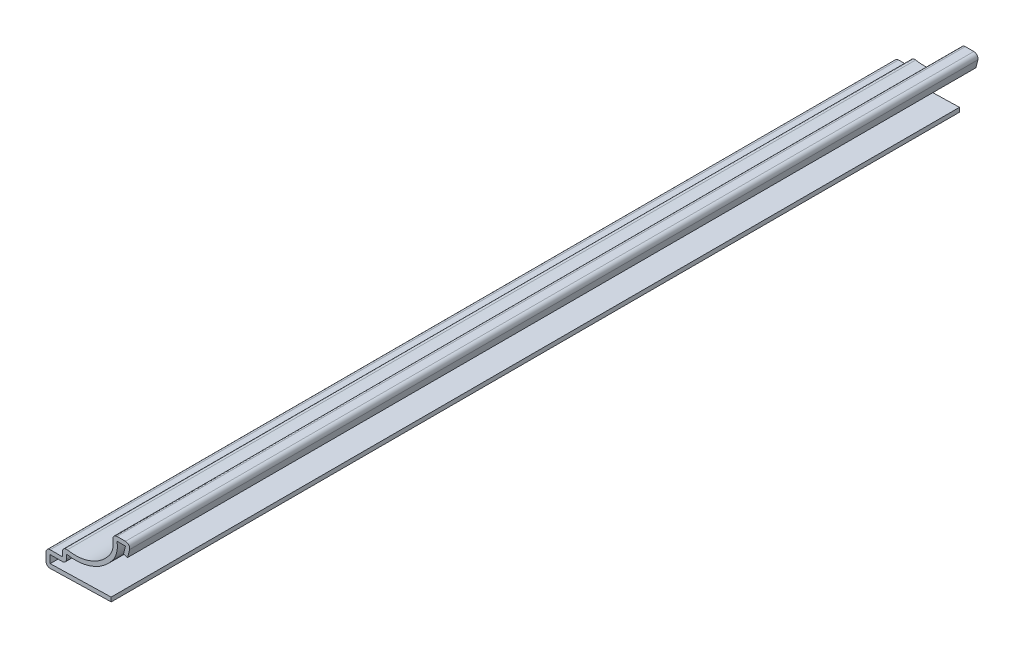
SolidWorks part; units mm, degrees
ref_plane "Front Plane" through (0, 0, 0) normal (0, 0, 1) x (1, 0, 0)
ref_plane "Top Plane" through (0, 0, 0) normal (0, 1, 0) x (1, 0, 0)
ref_plane "Right Plane" through (0, 0, 0) normal (1, 0, 0) x (0, 0, -1)
sketch "Sketch1" plane through (0, 0, 0) normal (0, 0, 1) x (1, 0, 0)
  line L0 (-4.7625, 0) -> (0, 0) construction
  line L1 (0, 0) -> (0, 11.7316) construction
  line L2 (0, 11.7316) -> (-0.7937, 11.7316) construction
  line L3 (-0.7937, 11.7316) -> (0, 14.9066)
  line L4 (0, 14.9066) -> (-4.7625, 14.9066)
  line L5 (-16.6687, 6.35) -> (-16.6687, 3.9688)
  line L6 (-16.6687, 3.9688) -> (-20.6375, 3.9688)
  line L7 (-20.6375, 3.9688) -> (-20.6375, 0)
  line L8 (-4.7625, 0) -> (-4.7625, 0.3969) construction
  line L9 (-20.6375, 0) -> (-4.7625, 0.3969)
  arc A0 (-4.7625, 14.9066) -> (-5.2408, 9.9742) centre (-9.0498, 12.8329) cw
  arc A1 (-5.2408, 9.9742) -> (-16.6687, 6.35) centre (-13.4937, 16.1681) cw
  point P14 (0, 0)
  dimension "D6" = 4.7625
  dimension "D7" = 10.3187
  dimension "D1" = 20.6375
  dimension "D2" = 4.7625
  dimension "D3" = 11.9062
  dimension "D4" = 0.7937
  dimension "D5" = 3.175
  dimension "D8" = 14.9066
  dimension "D9" = 2.3813
  dimension "D10" = 3.9688
  dimension "D11" = 0.3969
  dimension "D12" = 15.875
  dimension "D13" = 3.175
extrude "Extrude-Thin1" add sketch "Sketch1" against normal blind 206.375 thin thin type one direction reverse wall 1.016
fillet "Fillet1" radius 1.016 6 edges at (-20.6375, 0, -103.1875) (-20.6375, 3.9688, -103.1875) (-15.6527, 2.9528, -103.1875) (-16.6687, 6.35, -103.1875) (-4.7625, 14.9066, -103.1875) (0, 14.9066, -103.1875)
